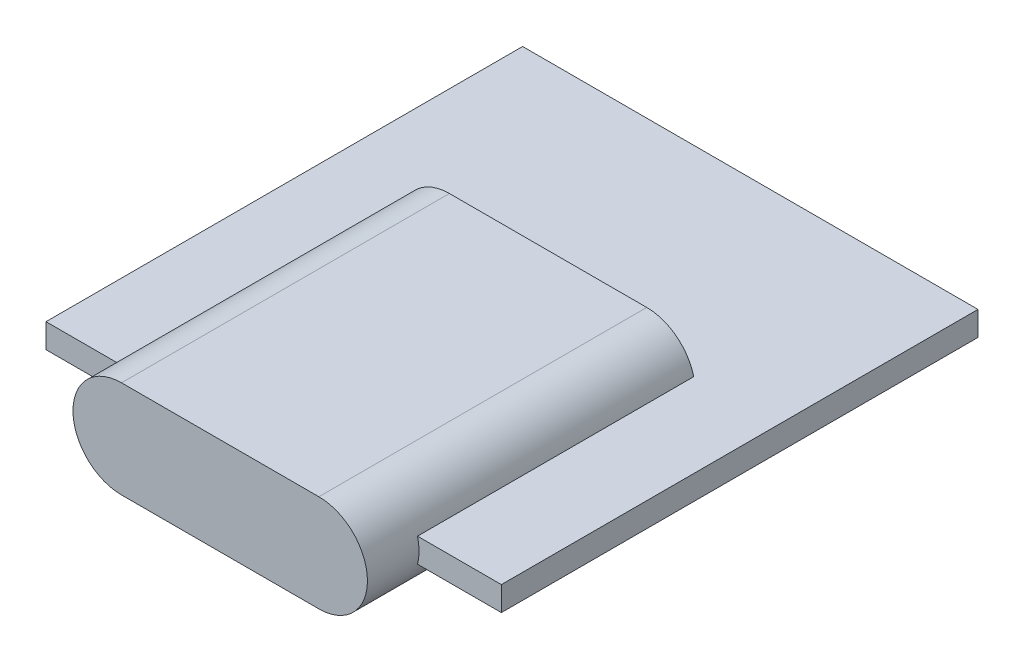
SolidWorks part; units mm, degrees
ref_plane "Front Plane" through (0, 0, 0) normal (0, 0, 1) x (1, 0, 0)
ref_plane "Top Plane" through (0, 0, 0) normal (0, 1, 0) x (1, 0, 0)
ref_plane "Right Plane" through (0, 0, 0) normal (1, 0, 0) x (0, 0, -1)
sketch "Sketch1" plane through (0, 0, 0) normal (0, 1, 0) x (1, 0, 0)
  line L1 (-7.1327, 7.6771) -> (7.8673, 7.6771)
  line L2 (-7.1327, 7.6771) -> (-7.1327, -8.0229)
  line L3 (-7.1327, -8.0229) -> (7.8673, -8.0229)
  line L4 (7.8673, 7.6771) -> (7.8673, -8.0229)
  dimension "D1" = 15.7
  dimension "D2" = 15
extrude "Boss-Extrude1" add sketch "Sketch1" along normal blind 0.8
ref_plane "Plane1" through (0, 0, 9.7229) normal (0, 0, 1) x (1, 0, 0)
sketch "Sketch2" plane through (0, 0, 9.7229) normal (0, 0, 1) x (1, 0, 0)
  line L0 (-2.9444, 0.4) -> (3.5556, 0.4) construction
  line L1 (-2.9444, 2) -> (3.5556, 2)
  line L2 (-2.9444, -1.2) -> (3.5556, -1.2)
  line L4 (-7.1327, 0) -> (7.8673, 0) construction
  arc A0 (-2.9444, 2) -> (-2.9444, -1.2) centre (-2.9444, 0.4) ccw
  arc A1 (3.5556, -1.2) -> (3.5556, 2) centre (3.5556, 0.4) ccw
  point P2 (0.3056, 0.4)
  dimension "D1" = 3.2
  dimension "D2" = 6.5
  dimension "D3" = 1.2
extrude "Boss-Extrude2" add sketch "Sketch2" against normal blind 10.8
